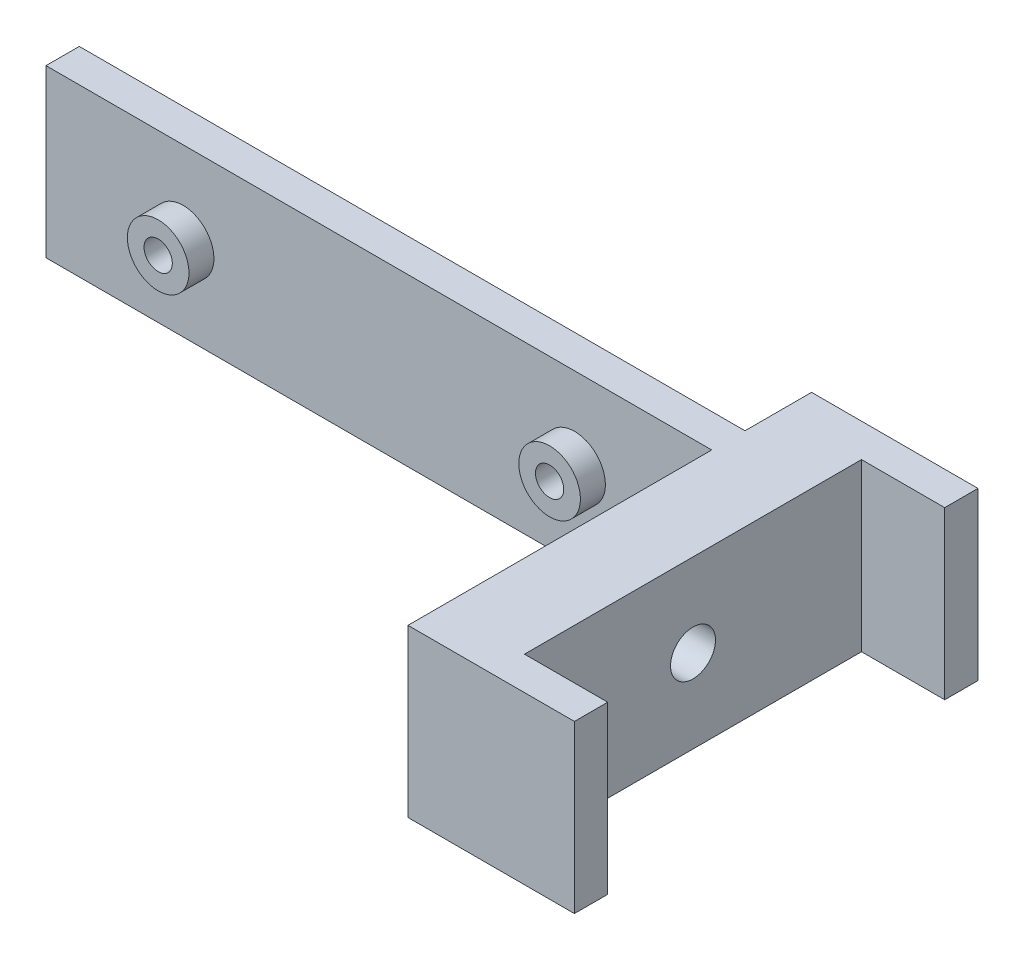
SolidWorks part; units mm, degrees
ref_plane "Front Plane" through (0, 0, 0) normal (0, 0, 1) x (1, 0, 0)
ref_plane "Top Plane" through (0, 0, 0) normal (0, 1, 0) x (1, 0, 0)
ref_plane "Right Plane" through (0, 0, 0) normal (1, 0, 0) x (0, 0, -1)
sketch "Sketch1" plane through (0, 0, 0) normal (0, 1, 0) x (1, 0, 0)
  line L1 (0, 0) -> (80, 0)
  line L2 (0, 0) -> (0, -4)
  line L3 (0, -4) -> (80, -4)
  line L4 (80, 0) -> (80, -4)
  line L5 (80, 8) -> (90, 8)
  line L6 (80, 8) -> (80, -40.5)
  line L7 (80, -40.5) -> (90, -40.5)
  line L8 (90, 8) -> (90, -40.5)
  line L9 (90, 8) -> (100, 8)
  line L10 (90, 8) -> (90, 4)
  line L11 (90, 4) -> (100, 4)
  line L12 (100, 8) -> (100, 4)
  line L13 (90, -40.5) -> (100, -40.5)
  line L14 (90, -40.5) -> (90, -36.5)
  line L15 (90, -36.5) -> (100, -36.5)
  line L16 (100, -40.5) -> (100, -36.5)
  dimension "D1" = 40.5
  dimension "D2" = 4
  dimension "D3" = 10
  dimension "D4" = 10
  dimension "D5" = 4
  dimension "D6" = 80
  dimension "D7" = 8
extrude "Boss-Extrude1" add sketch "Sketch1" along normal blind 20 contours L4 L1 L2 L3 | L8 L5 L6 L4 L7 | L12 L9 L8 L11 | L13 L16 L15 L8
sketch "Sketch2" plane through (90, 0, 0) normal (1, 0, 0) x (0, 0, -1)
  line L0 (-36.5, 10) -> (4, 10) construction
  line L1 (-36.5, 20) -> (-36.5, 0) construction
  line L2 (4, 20) -> (4, 0) construction
  circle A0 centre (-16.25, 10) radius 2.7
  dimension "D1" = 5.4
extrude "Cut-Extrude2" cut sketch "Sketch2" against normal up to next
sketch "Sketch4" plane through (0, 0, 4) normal (0, 0, 1) x (1, 0, 0)
  line L0 (40, 0) -> (40, 20) construction
  line L3 (0, 0) -> (80, 0) construction
  line L4 (0, 20) -> (80, 20) construction
  line L5 (40, 10) -> (18.18, 10) construction
  line L6 (40, 10) -> (61.82, 10) construction
  circle A0 centre (16.48, 10) radius 1.7
  circle A1 centre (63.52, 10) radius 1.7
  point P3 (30, 20)
  dimension "D2" = 3.4
  dimension "D1" = 21.82
extrude "Cut-Extrude3" cut sketch "Sketch4" against normal up to next
sketch "Sketch5" plane through (0, 0, 4) normal (0, 0, 1) x (1, 0, 0)
  circle A0 centre (63.52, 10) radius 1.7 construction
  circle A1 centre (16.48, 10) radius 1.7 construction
  circle A2 centre (63.52, 10) radius 1.7
  circle A3 centre (16.48, 10) radius 1.7
  circle A4 centre (16.48, 10) radius 3.7
  circle A5 centre (63.52, 10) radius 3.7
  dimension "D1" = 2
extrude "Boss-Extrude2" add sketch "Sketch5" along normal blind 3
sketch "Sketch6" plane through (80, 0, 0) normal (-1, 0, 0) x (0, 0, 1)
  circle A0 centre (16.25, 10) radius 4.3
  dimension "D1" = 8.6
extrude "Cut-Extrude4" cut sketch "Sketch6" against normal blind 5
sketch "Sketch7" plane through (0, 0, 0) normal (0, 0, -1) x (-1, 0, 0)
  line L1 (-60.77, 8.4123) -> (-60.77, 11.5877)
  line L2 (-60.77, 11.5877) -> (-63.52, 13.1754)
  line L3 (-63.52, 13.1754) -> (-66.27, 11.5877)
  line L4 (-66.27, 11.5877) -> (-66.27, 8.4123)
  line L5 (-66.27, 8.4123) -> (-63.52, 6.8246)
  line L6 (-63.52, 6.8246) -> (-60.77, 8.4123)
  line L7 (-13.73, 8.4123) -> (-13.73, 11.5877)
  line L8 (-13.73, 11.5877) -> (-16.48, 13.1754)
  line L9 (-16.48, 13.1754) -> (-19.23, 11.5877)
  line L10 (-19.23, 11.5877) -> (-19.23, 8.4123)
  line L11 (-19.23, 8.4123) -> (-16.48, 6.8246)
  line L12 (-16.48, 6.8246) -> (-13.73, 8.4123)
  circle A0 centre (-63.52, 10) radius 2.75 construction
  circle A1 centre (-16.48, 10) radius 2.75 construction
  dimension "D1" = 5.5
  dimension "D2" = 5.5
extrude "Cut-Extrude5" cut sketch "Sketch7" against normal blind 3
